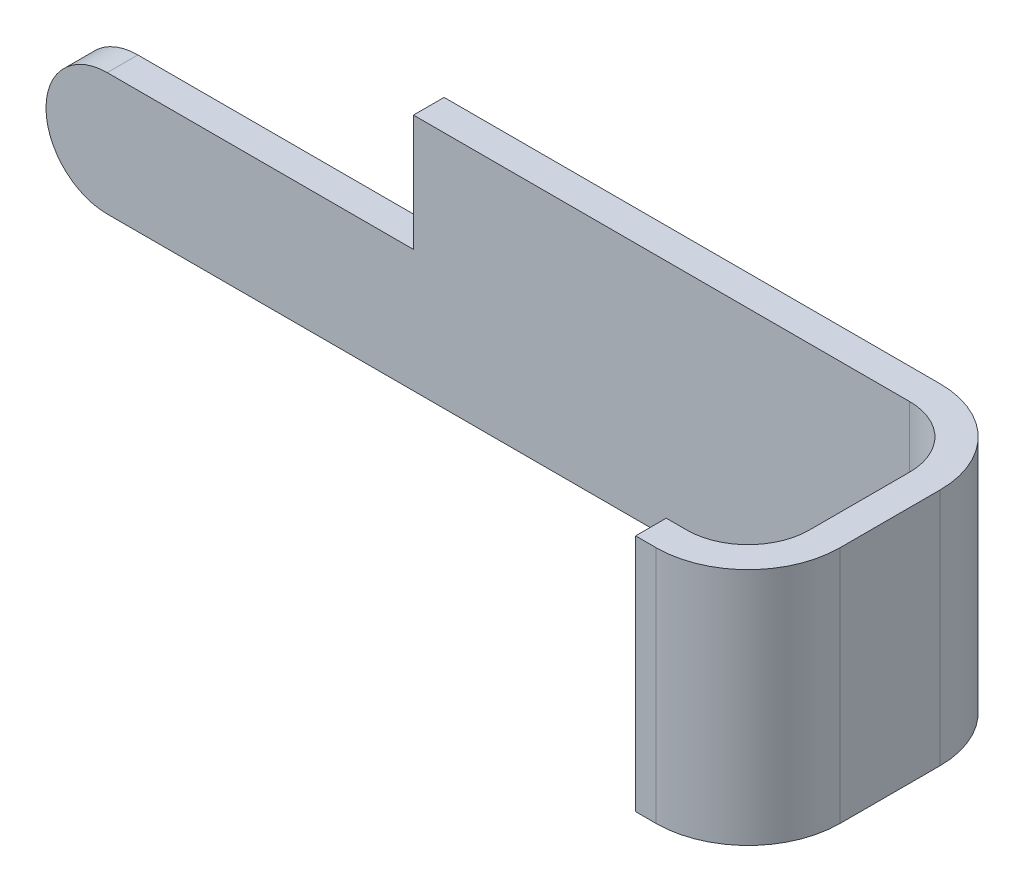
SolidWorks part; units mm, degrees
ref_plane "前视基准面" through (0, 0, 0) normal (0, 0, 1) x (1, 0, 0)
ref_plane "上视基准面" through (0, 0, 0) normal (0, 1, 0) x (1, 0, 0)
ref_plane "右视基准面" through (0, 0, 0) normal (1, 0, 0) x (0, 0, -1)
ref_plane "基准面4" through (0, 0, -0.25) normal (0, 0, -1) x (-1, 0, 0)
sketch "草图1" plane through (0, 0, -0.25) normal (0, 0, -1) x (-1, 0, 0)
  line L0 (0.486, 1) -> (-6.814, 1)
  line L1 (-6.814, 1) -> (-6.814, 0)
  line L2 (-6.814, 0) -> (0.486, 0)
  arc A0 (0.486, 0) -> (0.486, 1) centre (0.486, 0.5) ccw
extrude "凸台-拉伸1" add sketch "草图1" against normal blind 0.25
sketch "草图2" plane through (0, 1, 0) normal (0, 1, 0) x (-1, 0, 0)
  line L0 (-6.814, 0) -> (-2.014, 0)
  line L1 (-2.014, 0) -> (-2.014, -0.25)
  line L2 (-2.014, -0.25) -> (-6.814, -0.25)
  line L3 (-6.814, -0.25) -> (-6.814, 0)
extrude "凸台-拉伸2" add sketch "草图2" along normal blind 0.95
sketch "草图3" plane through (0, 0, 0) normal (0, 0, 1) x (1, 0, 0)
  line L0 (6.564, 1.95) -> (6.814, 1.95)
  line L1 (6.814, 1.95) -> (6.814, 0)
  line L2 (6.814, 0) -> (6.564, 0)
  line L3 (6.564, 0) -> (6.564, 1.95)
extrude "凸台-拉伸3" add sketch "草图3" along normal blind 2.0683
sketch "草图4" plane through (6.564, 0, 0) normal (-1, 0, 0) x (0, 0, 1)
  line L0 (2.0683, 1.95) -> (2.0683, 0)
  line L1 (2.0683, 0) -> (1.8183, 0)
  line L2 (1.8183, 0) -> (1.8183, 1.95)
  line L3 (1.8183, 1.95) -> (2.0683, 1.95)
extrude "凸台-拉伸4" add sketch "草图4" along normal blind 0.6683
fillet "圆角1" radius 0.5 2 edges at (6.564, 0.975, 0) (6.564, 0.975, 1.8183)
fillet "圆角2" radius 0.75 2 edges at (6.814, 0.975, -0.25) (6.814, 0.975, 2.0683)
